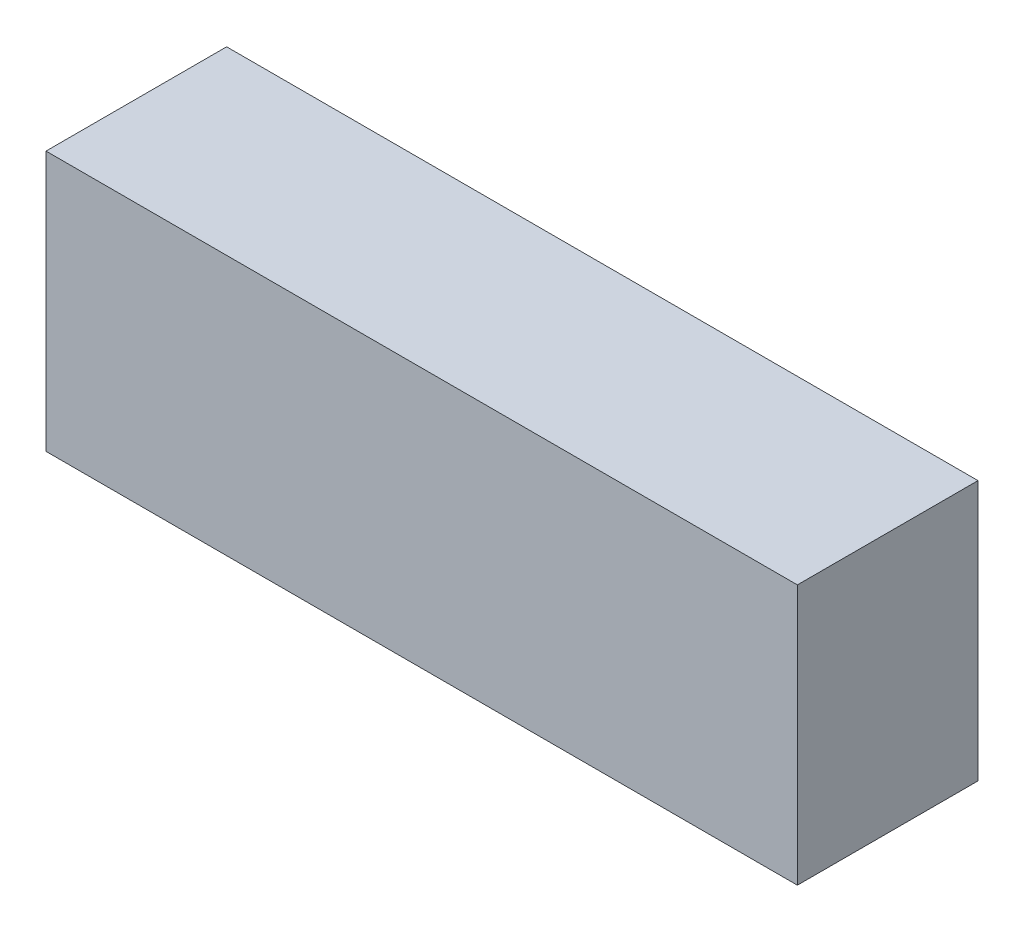
SolidWorks part; units mm, degrees
ref_plane "Front Plane" through (0, 0, 0) normal (0, 0, 1) x (1, 0, 0)
ref_plane "Top Plane" through (0, 0, 0) normal (0, 1, 0) x (1, 0, 0)
ref_plane "Right Plane" through (0, 0, 0) normal (1, 0, 0) x (0, 0, -1)
sketch "Sketch1" plane through (0, 0, 0) normal (0, 0, 1) x (1, 0, 0)
  line L1 (52, -18) -> (-52, -18)
  line L2 (52, -18) -> (52, 18)
  line L3 (52, 18) -> (-52, 18)
  line L4 (-52, -18) -> (-52, 18)
  line L5 (52, -18) -> (-52, 18) construction
  line L6 (52, 18) -> (-52, -18) construction
  point P0 (0, 0)
  dimension "D1" = 104
  dimension "D2" = 36
extrude "Boss-Extrude1" add sketch "Sketch1" along normal blind 25
